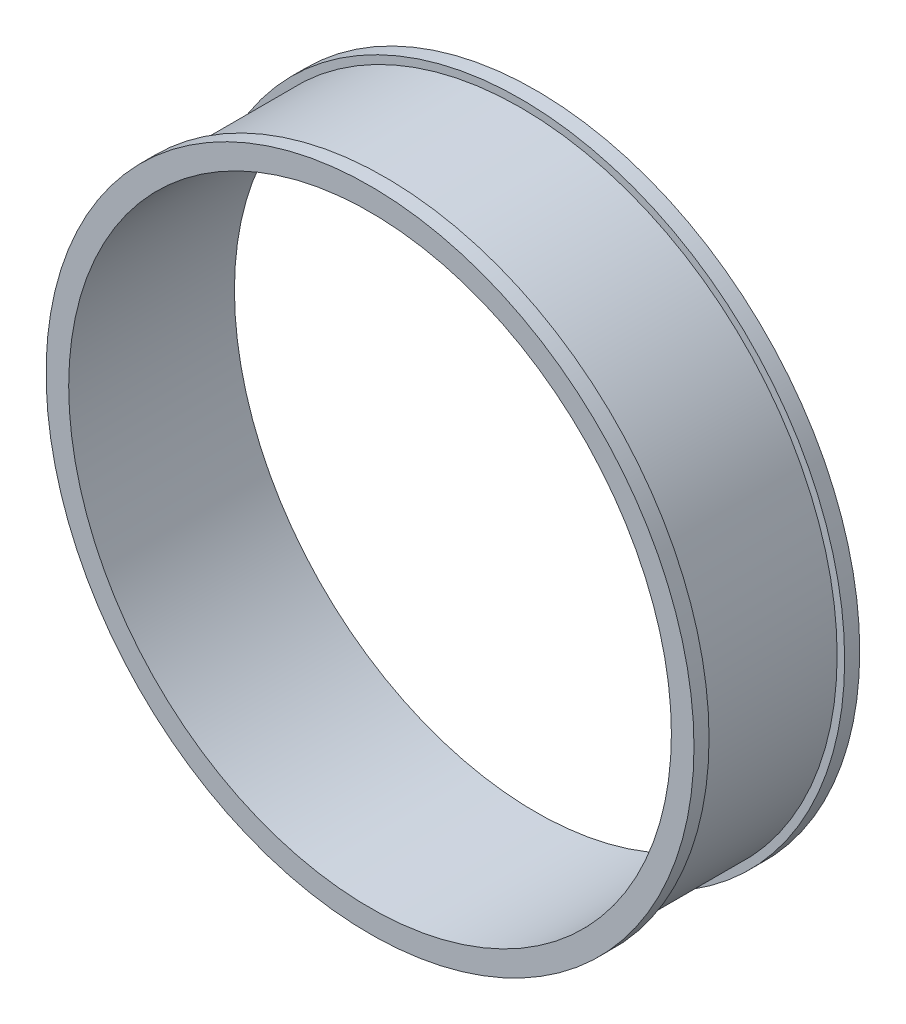
SolidWorks part; units mm, degrees
ref_plane "Front Plane" through (0, 0, 0) normal (0, 0, 1) x (1, 0, 0)
ref_plane "Top Plane" through (0, 0, 0) normal (0, 1, 0) x (1, 0, 0)
ref_plane "Right Plane" through (0, 0, 0) normal (1, 0, 0) x (0, 0, -1)
sketch "Sketch2" plane through (0, 0, 0) normal (0, 1, 0) x (1, 0, 0)
  line L0 (0, 0) -> (-244.938, 0) construction
  line L1 (-210, 45) -> (-215, 45)
  line L2 (-210, -45) -> (-215, -45)
  line L3 (-215, -45) -> (-215, -55)
  line L4 (-215, -55) -> (-200, -55)
  line L5 (-210, -45) -> (-210, 45)
  line L6 (-215, 45) -> (-215, 55)
  line L7 (-215, 55) -> (-200, 55)
  line L8 (-200, 55) -> (-200, -55)
  line L9 (0, -131.757) -> (0, 80.0096) construction
  point P6 (-200, 0)
  point P8 (-210, 0)
  dimension "D1" = 45
  dimension "D2" = 10
  dimension "D3" = 15
  dimension "D4" = 10
  dimension "D5" = 200
revolve "Revolve1" add sketch "Sketch2" angle 360 about L9
